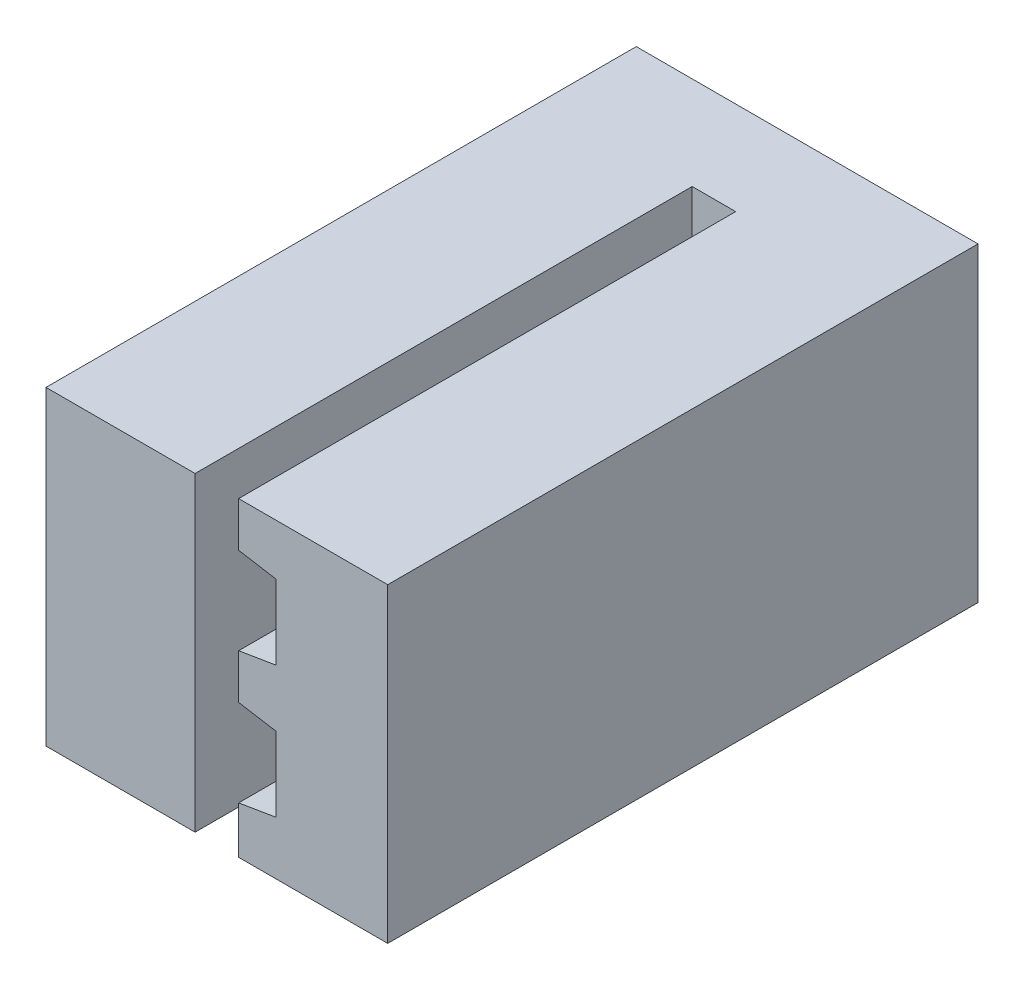
SolidWorks part; units mm, degrees
ref_plane "Alzado" through (0, 0, 0) normal (0, 0, 1) x (1, 0, 0)
ref_plane "Planta" through (0, 0, 0) normal (0, 1, 0) x (1, 0, 0)
ref_plane "Vista lateral" through (0, 0, 0) normal (1, 0, 0) x (0, 0, -1)
sketch "Croquis1" plane through (0, 0, 0) normal (0, 0, 1) x (1, 0, 0)
  line L0 (0, 7.1589) -> (0, 6.4)
  line L1 (0, 7.1589) -> (2.4, 7.1589)
  line L2 (-0.7, 7.1589) -> (-3.1, 7.1589)
  line L3 (-0.7, 7.1589) -> (-0.7, 0)
  line L4 (-0.7, 0) -> (-3.1, 0)
  line L5 (-3.1, 7.1589) -> (-3.1, 0)
  line L6 (0, 6.4) -> (0.6, 6.3)
  line L7 (0.6, 6.3) -> (0.6, 5.1)
  line L8 (0.6, 5.1) -> (0, 5)
  line L13 (0, 5) -> (0, 4.2794)
  line L14 (0, 4.2794) -> (0.6, 4.1794)
  line L15 (0.6, 4.1794) -> (0.6, 2.9794)
  line L16 (0.6, 2.9794) -> (0, 2.8794)
  line L17 (0, 2.8794) -> (0, 2.1589)
  line L18 (0, 2.1589) -> (0.6, 2.0589)
  line L19 (0.6, 2.0589) -> (0.6, 0.8589)
  line L20 (0.6, 0.8589) -> (0, 0.7589)
  line L21 (0, 0.7589) -> (0, 0)
  line L23 (0, 0) -> (2.4, 0)
  line L24 (2.4, 0) -> (2.4, 7.1589)
  dimension "D1" = 7.1589
  dimension "D2" = 0.7589
  dimension "D3" = 1.2
  dimension "D4" = 0.6
  dimension "D5" = 0.8589
  dimension "D6" = 2.4
  dimension "D7" = 5.5
  dimension "D8" = 0.7
  dimension "D9" = 0.7589
extrude "Saliente-Extruir1" add sketch "Croquis1" along normal blind 8
sketch "Croquis2" plane through (0, 0, 0) normal (0, 0, -1) x (-1, 0, 0)
  line L1 (-2.4, 7.1589) -> (3.1, 7.1589)
  line L2 (-2.4, 7.1589) -> (-2.4, 0)
  line L3 (-2.4, 0) -> (3.1, 0)
  line L4 (3.1, 7.1589) -> (3.1, 0)
extrude "Saliente-Extruir2" add sketch "Croquis2" along normal blind 1.5
sketch "Croquis3" plane through (0, 0, 8) normal (0, 0, 1) x (1, 0, 0)
  line L0 (2.4, 0) -> (2.4, 7.1589) construction
  line L1 (-3.1, 7.1589) -> (2.4, 7.1589)
  line L2 (-3.1, 7.1589) -> (-3.1, 5)
  line L3 (-3.1, 5) -> (2.4, 5)
  line L4 (2.4, 7.1589) -> (2.4, 5)
extrude "Cortar-Extruir1" cut sketch "Croquis3" against normal through all
